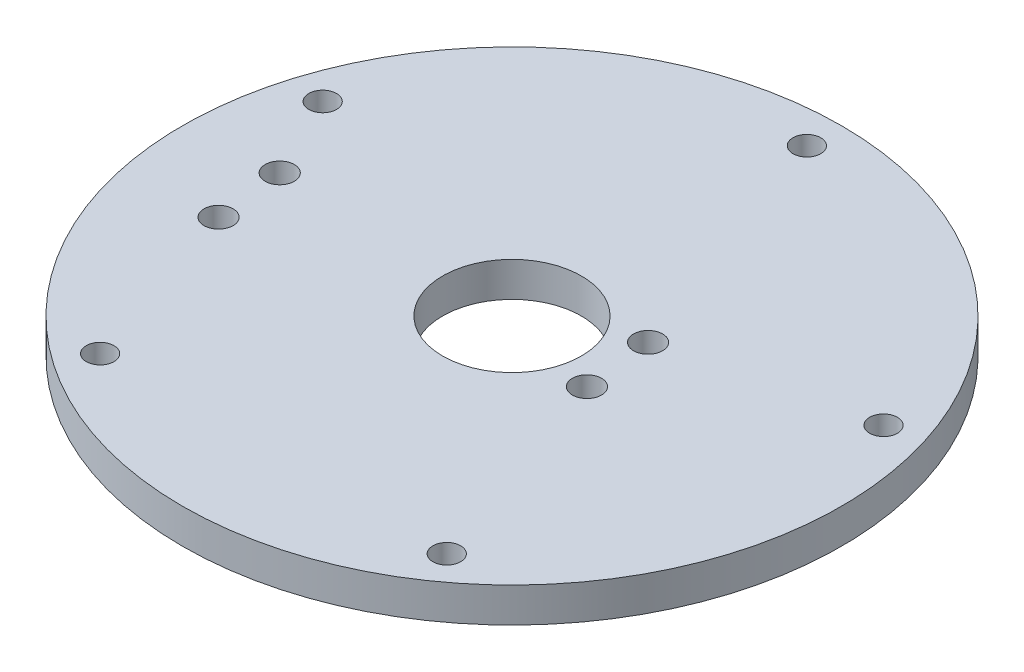
SolidWorks part; units mm, degrees
material "Acrylic (Medium-high impact)"
ref_plane "Front Plane" through (0, 0, 0) normal (0, 0, 1) x (1, 0, 0)
ref_plane "Top Plane" through (0, 0, 0) normal (0, 1, 0) x (1, 0, 0)
ref_plane "Right Plane" through (0, 0, 0) normal (1, 0, 0) x (0, 0, -1)
sketch "Sketch1" plane through (0, 0, 0) normal (0, 1, 0) x (1, 0, 0)
  circle A0 centre (0, 0) radius 47.5
  circle A1 centre (0, 0) radius 42.5 construction
  circle A2 centre (0, 42.5) radius 2
  circle A3 centre (40.4199, 13.1332) radius 2
  circle A4 centre (24.9809, -34.3832) radius 2
  circle A5 centre (-24.9809, -34.3832) radius 2
  circle A6 centre (-40.4199, 13.1332) radius 2
  circle A8 centre (0, 0) radius 10
  circle A9 centre (-34.595, 1.1161) radius 2.1
  circle A10 centre (14.2251, -3.4218) radius 2.1
  circle A11 centre (-33.4703, -8.8204) radius 2.1
  circle A12 centre (13.1004, 6.5148) radius 2.1
  point P17 (0, 0)
  dimension "D1" = 95
  dimension "D2" = 85
  dimension "D3" = 4
  dimension "D5" = 20
  dimension "D6" = 4.2
  dimension "D4" = 5
extrude "Boss-Extrude1" add sketch "Sketch1" along normal blind 5
